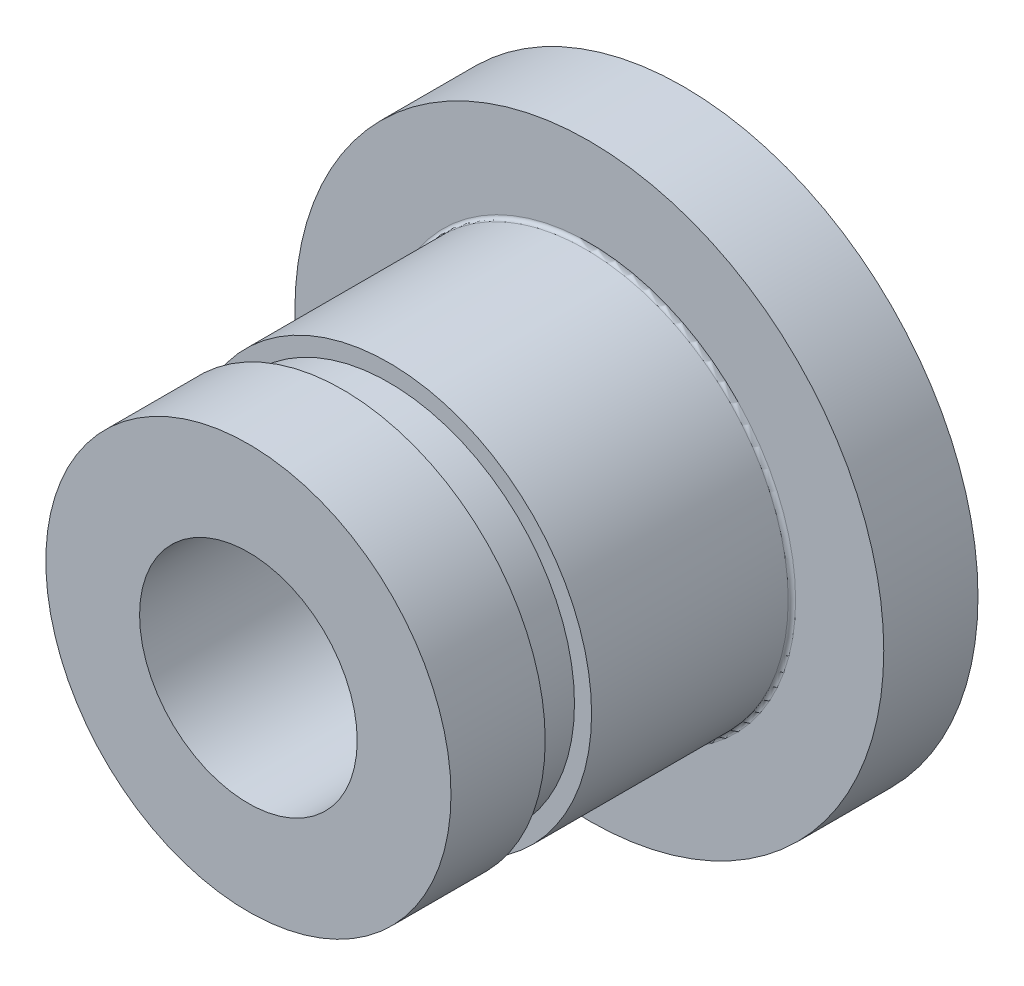
SolidWorks part; units mm, degrees
material "AISI 4340 Steel, normalized"
ref_plane "Front Plane" through (0, 0, 0) normal (0, 0, 1) x (1, 0, 0)
ref_plane "Top Plane" through (0, 0, 0) normal (0, 1, 0) x (1, 0, 0)
ref_plane "Right Plane" through (0, 0, 0) normal (1, 0, 0) x (0, 0, -1)
sketch "Sketch1" plane through (0, 0, 0) normal (1, 0, 0) x (0, 0, -1)
  line L0 (0, 2.9337) -> (11.73, 2.9337)
  line L1 (11.73, 2.9337) -> (11.73, 7.9375)
  line L2 (11.73, 7.9375) -> (9.19, 7.9375)
  line L3 (9.19, 7.9375) -> (9.19, 5.561)
  line L4 (9.09, 5.461) -> (3.79, 5.461)
  line L5 (3.79, 5.461) -> (3.79, 5)
  line L6 (3.79, 5) -> (2.54, 5)
  line L7 (2.54, 5) -> (2.54, 5.461)
  line L8 (2.54, 5.461) -> (0, 5.461)
  line L9 (0, 5.461) -> (0, 2.9337)
  line L10 (0, 0) -> (48.6316, 0) construction
  arc A0 (9.19, 5.561) -> (9.09, 5.461) centre (9.09, 5.561) cw
  dimension "D9" = 0.1
  dimension "D1" = 5.4
  dimension "D2" = 2.54
  dimension "D3" = 7.9375
  dimension "D4" = 2.9337
  dimension "D5" = 5.461
  dimension "D6" = 2.54
  dimension "D7" = 5
  dimension "D8" = 1.25
revolve "Revolve1" add sketch "Sketch1" angle 360 about L10
sketch "Sketch2" plane through (0, 0, 0) normal (0, 0, 1) x (1, 0, 0)
  line L0 (0, 7.9375) -> (0, -7.9375) construction
  line L1 (4.7, 2.7807) -> (4.7, -2.7807)
  line L2 (-4.7, 2.7807) -> (-4.7, -2.7807)
  circle A0 centre (0, 0) radius 7.9375 construction
  circle A1 centre (0, 0) radius 5.461 construction
  arc A2 (4.7, 2.7807) -> (-4.7, 2.7807) centre (0, 0) ccw
  arc A3 (-4.7, -2.7807) -> (4.7, -2.7807) centre (0, 0) ccw
  circle A5 centre (0, 0) radius 7.9375
  dimension "D1" = 9.4
extrude "Extrude1" [suppressed] cut sketch "Sketch2" against normal up to surface (8.65 mm away)
sketch "Sketch3" plane through (0, 0, -11.73) normal (0, 0, -1) x (-1, 0, 0)
  circle A0 centre (0, 0) radius 4 construction
  text T0 "C     " font "Century Gothic" height in points 10
  dimension "D1" = 8
extrude "Extrude2" [suppressed] cut sketch "Sketch3" against normal blind 0.1
